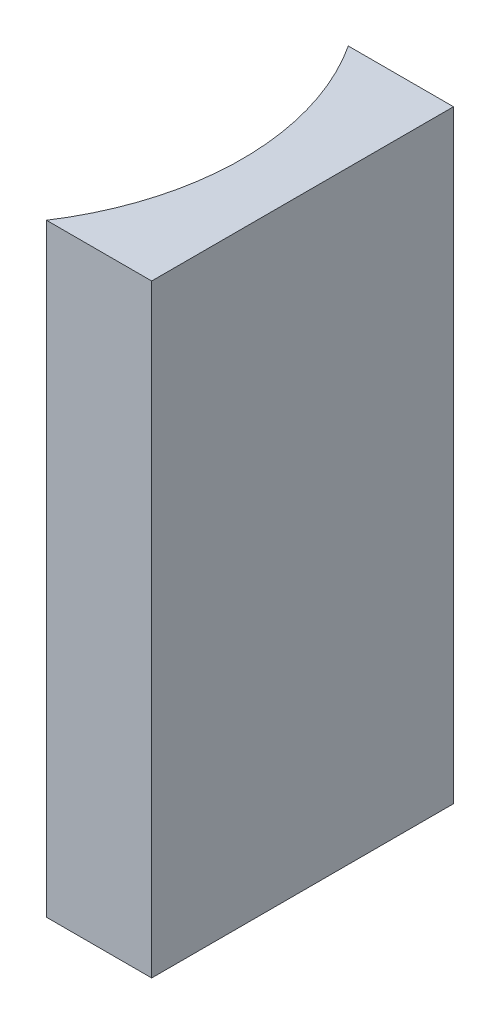
SolidWorks part; units mm, degrees
ref_plane "前视基准面" through (0, 0, 0) normal (0, 0, 1) x (1, 0, 0)
ref_plane "上视基准面" through (0, 0, 0) normal (0, 1, 0) x (1, 0, 0)
ref_plane "右视基准面" through (0, 0, 0) normal (1, 0, 0) x (0, 0, -1)
sketch "草图1" plane through (0, 0, 0) normal (0, 1, 0) x (1, 0, 0)
  line L0 (0, 0) -> (0, -10)
  line L1 (0, 0) -> (-3.485, 0)
  line L2 (0, -10) -> (-3.485, -10)
  line L3 (21.2259, -5) -> (-21.2259, -5) construction
  arc A0 (-3.485, -10) -> (-3.485, 0) centre (-11.16, -5) ccw
  point P7 (-2, -5)
  point P8 (0, -5)
  dimension "D2" = 9.16
  dimension "D3" = 2
  dimension "D1" = 10
extrude "凸台-拉伸1" add sketch "草图1" along normal blind 20
